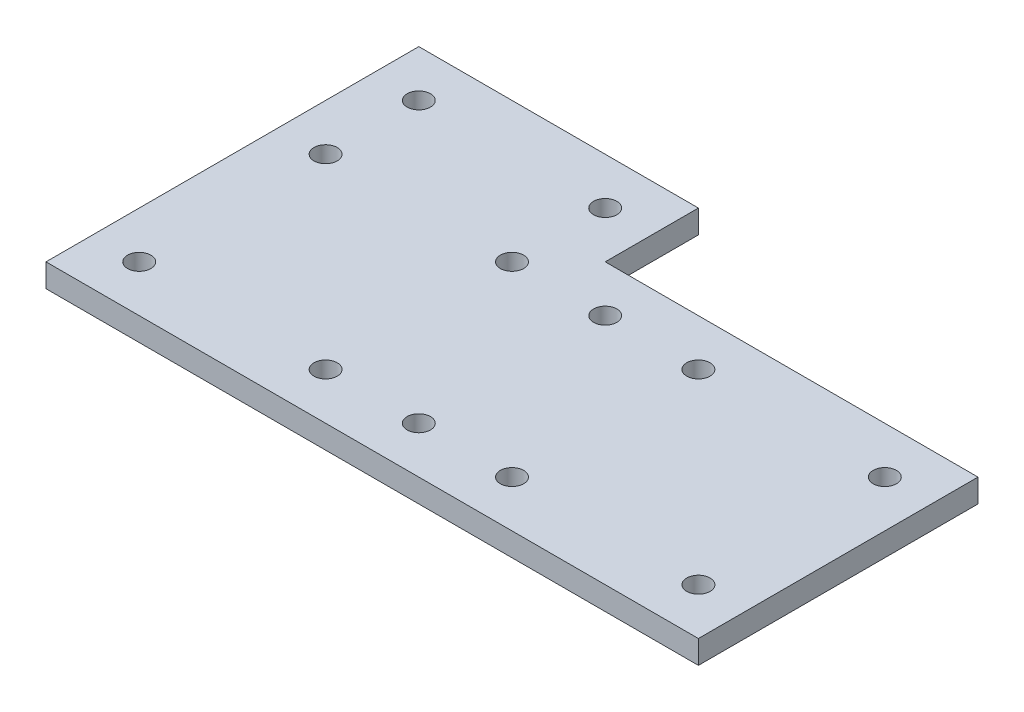
SolidWorks part; units mm, degrees
ref_plane "Front Plane" through (0, 0, 0) normal (0, 0, 1) x (1, 0, 0)
ref_plane "Top Plane" through (0, 0, 0) normal (0, 1, 0) x (1, 0, 0)
ref_plane "Right Plane" through (0, 0, 0) normal (1, 0, 0) x (0, 0, -1)
sketch "Sketch1" plane through (0, 0, 0) normal (0, 1, 0) x (1, 0, 0)
  line L0 (0, 50.8) -> (0, 0)
  line L1 (0, 0) -> (88.9, 0)
  line L2 (88.9, 0) -> (88.9, 38.1)
  line L3 (88.9, 38.1) -> (38.1, 38.1)
  line L4 (38.1, 38.1) -> (38.1, 50.8)
  line L5 (38.1, 50.8) -> (0, 50.8)
  dimension "D1" = 38.1
  dimension "D2" = 38.1
  dimension "D3" = 88.9
  dimension "D4" = 50.8
extrude "Boss-Extrude1" add sketch "Sketch1" along normal blind 3.175
sketch "Sketch2" plane through (0, 3.175, 0) normal (0, 1, 0) x (1, 0, 0)
  line L0 (88.9, 38.1) -> (38.1, 38.1) construction
  line L1 (6.35, 44.45) -> (31.75, 44.45) construction
  line L2 (6.35, 44.45) -> (6.35, 6.35) construction
  line L3 (6.35, 6.35) -> (31.75, 6.35) construction
  line L4 (31.75, 44.45) -> (31.75, 6.35) construction
  line L5 (6.35, 6.35) -> (82.55, 6.35) construction
  line L6 (6.35, 6.35) -> (6.35, 31.75) construction
  line L7 (6.35, 31.75) -> (82.55, 31.75) construction
  line L8 (82.55, 6.35) -> (82.55, 31.75) construction
  line L9 (38.1, 38.1) -> (38.1, 50.8) construction
  line L10 (38.1, 50.8) -> (0, 50.8) construction
  line L11 (6.35, 31.75) -> (31.75, 6.35) construction
  line L12 (31.75, 6.35) -> (57.15, 31.75) construction
  line L13 (57.15, 31.75) -> (82.55, 6.35) construction
  line L14 (88.9, 0) -> (88.9, 38.1) construction
  line L15 (38.1, 38.1) -> (38.1, 0) construction
  line L16 (0, 0) -> (88.9, 0) construction
  line L17 (44.45, 38.1) -> (44.45, -0.0007) construction
  line L18 (57.15, 31.75) -> (57.15, 6.35) construction
  circle A0 centre (6.35, 44.45) radius 1.5875
  circle A1 centre (31.75, 44.45) radius 1.5875
  circle A2 centre (31.75, 31.75) radius 1.5875
  circle A3 centre (6.35, 31.75) radius 1.5875
  circle A4 centre (6.35, 6.35) radius 1.5875
  circle A5 centre (31.75, 6.35) radius 1.5875
  circle A6 centre (82.55, 6.35) radius 1.5875
  circle A7 centre (82.55, 31.75) radius 1.5875
  circle A8 centre (57.15, 31.75) radius 1.5875
  circle A9 centre (57.15, 6.35) radius 1.5875
  circle A10 centre (44.45, 6.35) radius 1.5875
  circle A11 centre (44.45, 31.75) radius 1.5875
  point P39 (31.75, 31.75)
  dimension "D9" = 3.175
  dimension "D1" = 25.4
  dimension "D2" = 25.4
  dimension "D3" = 6.35
  dimension "D4" = 6.35
  dimension "D5" = 6.35
  dimension "D6" = 25.4
  dimension "D7" = 6.35
  dimension "D8" = 6.35
extrude "Cut-Extrude1" cut sketch "Sketch2" against normal through all
